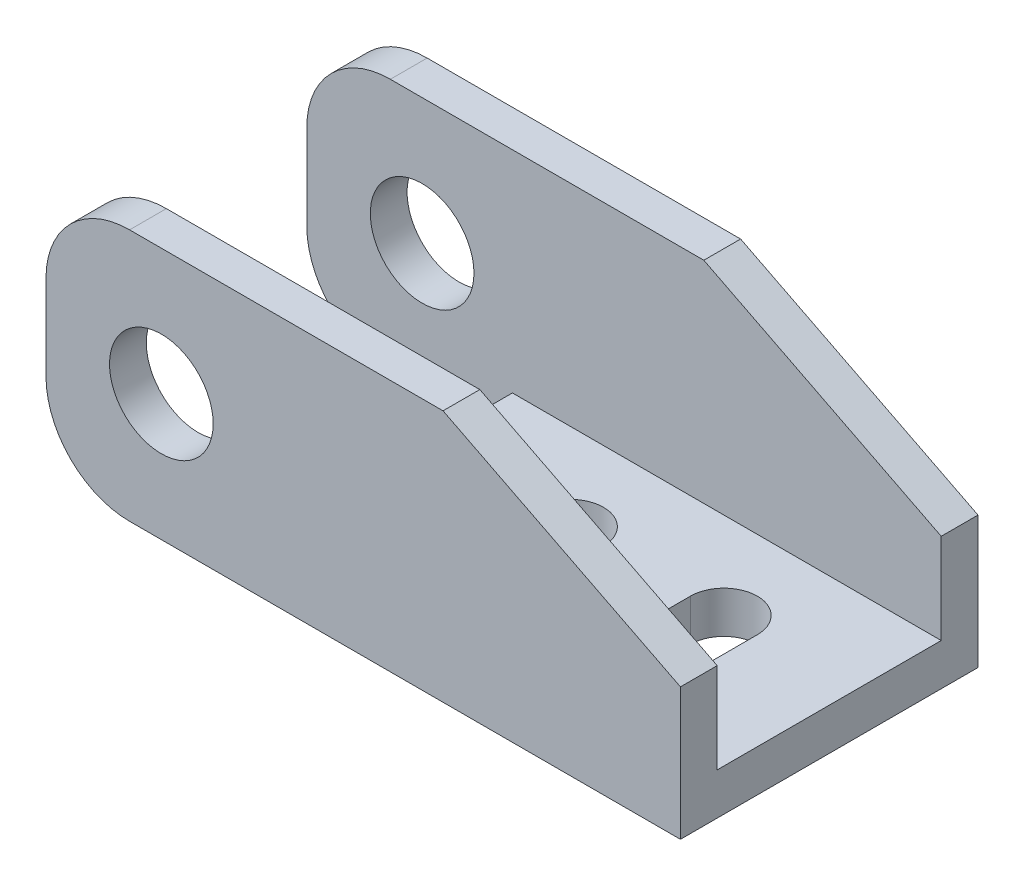
SolidWorks part; units mm, degrees
ref_plane "Alzado" through (0, 0, 0) normal (0, 0, 1) x (1, 0, 0)
ref_plane "Planta" through (0, 0, 0) normal (0, 1, 0) x (1, 0, 0)
ref_plane "Vista lateral" through (0, 0, 0) normal (1, 0, 0) x (0, 0, -1)
sketch "Croquis1" plane through (0, 0, 0) normal (0, 1, 0) x (1, 0, 0)
  line L1 (-12.825, -8.9) -> (12.825, -8.9)
  line L2 (-12.825, -8.9) -> (-12.825, 8.9)
  line L3 (-12.825, 8.9) -> (12.825, 8.9)
  line L4 (12.825, -8.9) -> (12.825, 8.9)
  line L5 (-12.825, -8.9) -> (12.825, 8.9) construction
  line L6 (-12.825, 8.9) -> (12.825, -8.9) construction
  point P0 (0, 0)
  dimension "D1" = 25.65
  dimension "D2" = 17.8
extrude "Saliente-Extruir1" add sketch "Croquis1" along normal blind 2.5
sketch "Croquis2" plane through (0, 0, 8.9) normal (0, 0, 1) x (1, 0, 0)
  line L0 (-25.125, 0) -> (12.825, 0)
  line L1 (-25.125, 0) -> (-25.125, 15.1)
  line L2 (-25.125, 15.1) -> (-1.375, 15.1)
  line L3 (-1.375, 15.1) -> (12.825, 7.9)
  line L4 (12.825, 7.9) -> (12.825, 0)
  dimension "D1" = 37.95
  dimension "D2" = 15.1
  dimension "D3" = 14.2
  dimension "D4" = 7.9
extrude "Saliente-Extruir2" add sketch "Croquis2" against normal blind 2.2
mirror "Simetría1" about plane through (0, 0, 0) normal (0, 0, 1) of "Saliente-Extruir2"
sketch "Croquis3" plane through (0, 0, 8.9) normal (0, 0, 1) x (1, 0, 0)
  line L0 (-25.125, 15.1) -> (-25.125, 0) construction
  line L1 (-18.225, 7.55) -> (-25.125, 7.55) construction
  circle A0 centre (-18.225, 7.55) radius 3.1
  dimension "D1" = 6.2
  dimension "D2" = 6.9
extrude "Cortar-Extruir1" cut sketch "Croquis3" against normal through all
sketch "Croquis4" plane through (0, 0, 0) normal (0, -1, 0) x (1, 0, 0)
  line L0 (-4.175, 1.5) -> (-4.175, -1.5) construction
  line L1 (-2.175, 1.5) -> (-2.175, -1.5)
  line L2 (-6.175, 1.5) -> (-6.175, -1.5)
  line L3 (-4.175, 0) -> (-12.825, 0) construction
  line L4 (-12.825, -6.7) -> (-12.825, 6.7) construction
  line L5 (5.025, -1.5) -> (5.025, 1.5) construction
  line L6 (3.025, -1.5) -> (3.025, 1.5)
  line L7 (7.025, -1.5) -> (7.025, 1.5)
  line L8 (12.825, 8.9) -> (12.825, -8.9) construction
  arc A0 (-2.175, 1.5) -> (-6.175, 1.5) centre (-4.175, 1.5) ccw
  arc A1 (-6.175, -1.5) -> (-2.175, -1.5) centre (-4.175, -1.5) ccw
  arc A2 (3.025, -1.5) -> (7.025, -1.5) centre (5.025, -1.5) ccw
  arc A3 (7.025, 1.5) -> (3.025, 1.5) centre (5.025, 1.5) ccw
  point P2 (-4.175, 0)
  point P13 (5.025, 0)
  dimension "D1" = 2
  dimension "D2" = 3
  dimension "D3" = 5.2
  dimension "D4" = 5.8
extrude "Cortar-Extruir2" cut sketch "Croquis4" against normal through all
fillet "Redondeo1" radius 5 4 edges at (-25.125, 0, -7.8) (-25.125, 15.1, -7.8) (-25.125, 15.1, 7.8) (-25.125, 0, 7.8)
